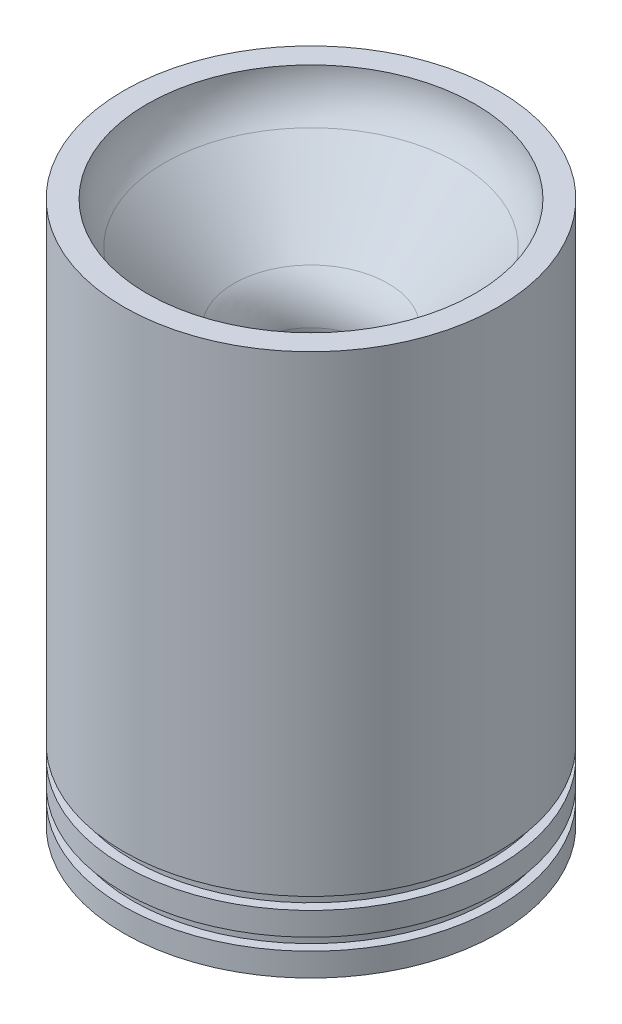
SolidWorks part; units mm, degrees
ref_plane "Front Plane" through (0, 0, 0) normal (0, 0, 1) x (1, 0, 0)
ref_plane "Top Plane" through (0, 0, 0) normal (0, 1, 0) x (1, 0, 0)
ref_plane "Right Plane" through (0, 0, 0) normal (1, 0, 0) x (0, 0, -1)
sketch "Sketch1" plane through (0, 0, 0) normal (0, 0, 1) x (1, 0, 0)
  line L0 (-51.1302, 0) -> (-51.1302, -128.7646)
  line L1 (-51.1302, -148.0686) -> (-44.45, -148.0686)
  line L2 (-44.45, -148.0686) -> (-16.4776, -43.6741)
  line L5 (-44.7802, 0) -> (-51.1302, 0)
  line L6 (0, 0) -> (0, -59.8568) construction
  line L7 (-51.1302, -148.0686) -> (-51.1302, -141.7186)
  line L8 (-51.1302, -141.7186) -> (-48.5902, -141.7186)
  line L9 (-48.5902, -141.7186) -> (-48.5902, -138.4166)
  line L10 (-48.5902, -138.4166) -> (-51.1302, -138.4166)
  line L11 (-51.1302, -138.4166) -> (-51.1302, -132.0666)
  line L12 (-51.1302, -132.0666) -> (-48.5902, -132.0666)
  line L13 (-48.5902, -132.0666) -> (-48.5902, -128.7646)
  line L14 (-48.5902, -128.7646) -> (-51.1302, -128.7646)
  line L15 (-40.0189, -11.4947) -> (-21.0173, -30.4964)
  line L16 (-44.7802, 0) -> (-44.7802, 6.9427) construction
  arc A0 (-44.7802, 0) -> (-40.0189, -11.4947) centre (-28.5242, 0) ccw
  arc A1 (-21.0173, -30.4964) -> (-16.256, -41.9911) centre (-32.512, -41.9911) cw
  arc A2 (-16.256, -41.9911) -> (-16.4776, -43.6741) centre (-22.7584, -41.9911) cw
  point P22 (0, 0)
  point P24 (0, 0)
  point P25 (0, 0)
  point P26 (-17.1496, -42.7805)
  dimension "D7" = 16.256
  dimension "D13" = 6.5024
  dimension "D14" = 16.256
  dimension "D2" = 51.1302
  dimension "D3" = 44.45
  dimension "D6" = 6.35
  dimension "D8" = 3.302
  dimension "D9" = 2.54
  dimension "D10" = 6.35
  dimension "D11" = 3.302
  dimension "D12" = 6.35
  dimension "D4" = 105
  dimension "D5" = 45
  dimension "D15" = 16.256
revolve "Revolve1" add sketch "Sketch1" angle 360 about L6
equation "\"D11@Sketch1\"=\"D8@Sketch1\""
